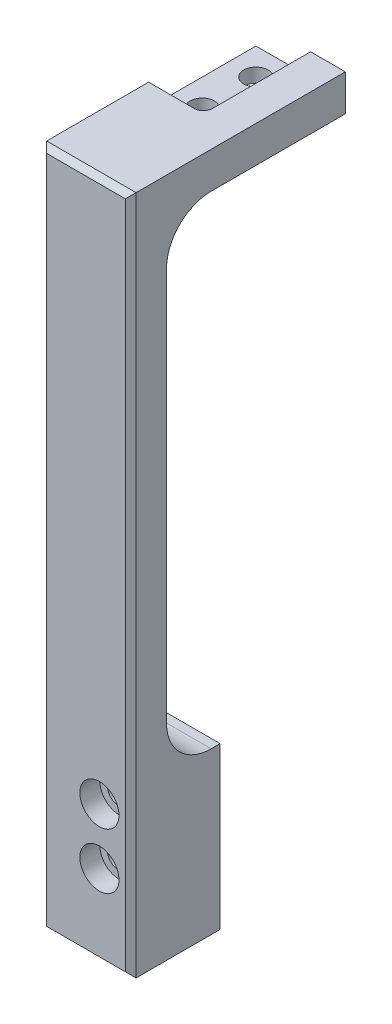
SolidWorks part; units mm, degrees
material "COPPER"
ref_plane "Front Plane" through (0, 0, 0) normal (0, 0, 1) x (1, 0, 0)
ref_plane "Top Plane" through (0, 0, 0) normal (0, 1, 0) x (1, 0, 0)
ref_plane "Right Plane" through (0, 0, 0) normal (1, 0, 0) x (0, 0, -1)
sketch "Sketch1" plane through (0, 0, 0) normal (0, 0, 1) x (1, 0, 0)
  line L1 (0, 0) -> (12.7, 0)
  line L2 (0, 0) -> (0, -96.5962)
  line L3 (0, -96.5962) -> (12.7, -96.5962)
  line L4 (12.7, 0) -> (12.7, -96.5962)
  dimension "D1" = 96.5962
  dimension "D2" = 12.7
extrude "Extrude1" add sketch "Sketch1" along normal blind 5.08
sketch "Sketch2" plane through (0, 0, 0) normal (0, 0, -1) x (-1, 0, 0)
  line L0 (0, 0) -> (0, -96.5962) construction
  line L1 (-12.7, 0) -> (0, 0)
  line L2 (-12.7, 0) -> (-12.7, -5.165)
  line L3 (-12.7, -5.165) -> (0, -5.165)
  line L4 (0, 0) -> (0, -5.165)
extrude "Extrude2" add sketch "Sketch2" along normal blind 25.4
hole_wizard "#4 Clearance Hole1" positions "Sketch9" profile "Sketch8" hole size "#4" standard "Ansi Inch" end condition through all
sketch "Sketch9" plane through (0, 0, 0) normal (0, 1, 0) x (-1, 0, 0)
  line L0 (-3.81, -25.4) -> (-3.81, 5.08) construction
  line L1 (0, -25.4) -> (-12.7, -25.4) construction
  line L5 (0, 5.08) -> (0, -25.4) construction
  point P0 (-3.81, -21.59)
  point P1 (-3.81, -13.97)
  dimension "D1" = 7.62
  dimension "D2" = 3.81
  dimension "D3" = 3.81
sketch "Sketch8" plane through (3.81, 0, -21.59) normal (1, 0, 0) x (0, 0, 1)
  line L0 (0, 0) -> (0, 96.5962)
  line L1 (0, 96.5962) -> (1.7272, 96.5962)
  line L2 (1.7272, 96.5962) -> (1.7272, 0)
  line L5 (1.7272, 0) -> (0, 0)
  line L11 (0, -6.35) -> (0, 107.95) construction
  dimension "Thru Hole Dia." = 3.4544
  dimension "Thru Hole Depth" = 96.5962
sketch "Sketch6" plane through (0, 0, 0) normal (0, 0, -1) x (-1, 0, 0)
  line L0 (0, -5.165) -> (0, -96.5962) construction
  line L1 (-12.7, -96.5962) -> (0, -96.5962)
  line L2 (-12.7, -96.5962) -> (-12.7, -73.7362)
  line L3 (-12.7, -73.7362) -> (0, -73.7362)
  line L4 (0, -96.5962) -> (0, -73.7362)
  dimension "D1" = 22.86
extrude "Extrude4" add sketch "Sketch6" along normal blind 7.62
sketch "Sketch7" plane through (0, 0, 0) normal (0, 1, 0) x (1, 0, 0)
  line L0 (0, 25.4) -> (12.7, 25.4) construction
  line L1 (-0.1524, 25.4) -> (7.7724, 25.4)
  line L2 (-0.1524, 25.4) -> (-0.1524, 10.16)
  line L3 (-0.1524, 10.16) -> (7.7724, 10.16)
  line L4 (7.7724, 25.4) -> (7.7724, 10.16)
  line L5 (3.81, 25.4) -> (3.81, 10.16) construction
  dimension "D1" = 7.9248
  dimension "D2" = 15.24
extrude "Extrude5" cut sketch "Sketch7" against normal blind 3.175
fillet "Fillet1" radius 1.27 1 edges at (7.7724, -1.5875, -10.16)
fillet "Fillet3" radius 6.35 2 edges at (6.35, -73.7362, 0)
chamfer "Chamfer1" distance 0.762 angle 45 4 edges at (0, -48.2981, 5.08) (6.35, -96.5962, 5.08) (12.7, -48.2981, 5.08) (6.35, 0, 5.08)
hole_wizard "CBORE for #4 Socket Head Cap Screw1" positions "Sketch15" profile "Sketch14" counterbore size "#4" standard "Ansi Inch" end condition through all
sketch "Sketch15" plane through (0, 0, 5.08) normal (0, 0, 1) x (1, 0, 0)
  line L0 (8.255, -77.047) -> (8.255, -84.9718) construction
  line L2 (12.7, 0) -> (12.7, -96.5962) construction
  line L3 (12.7, -96.5962) -> (0, -96.5962) construction
  point P0 (8.255, -84.9718)
  point P1 (8.255, -77.047)
  dimension "D1" = 7.9248
  dimension "D2" = 19.5492
  dimension "D3" = 4.445
sketch "Sketch14" plane through (8.255, -84.9718, 5.08) normal (1, 0, 0) x (0, -1, 0)
  line L0 (0, 0) -> (0, 30.48)
  line L1 (0, 30.48) -> (1.7272, 30.48)
  line L3 (1.7272, 30.48) -> (1.7272, 2.8448)
  line L4 (1.7272, 2.8448) -> (2.7788, 2.8448)
  line L5 (2.7788, 2.8448) -> (2.7788, 0)
  line L7 (2.7788, 0) -> (0, 0)
  line L11 (0, -6.35) -> (0, 107.95) construction
  dimension "Thru Hole Dia." = 3.4544
  dimension "Thru Hole Depth" = 30.48
  dimension "C'Bore Dia." = 5.5575
  dimension "C'Bore Depth" = 2.8448
